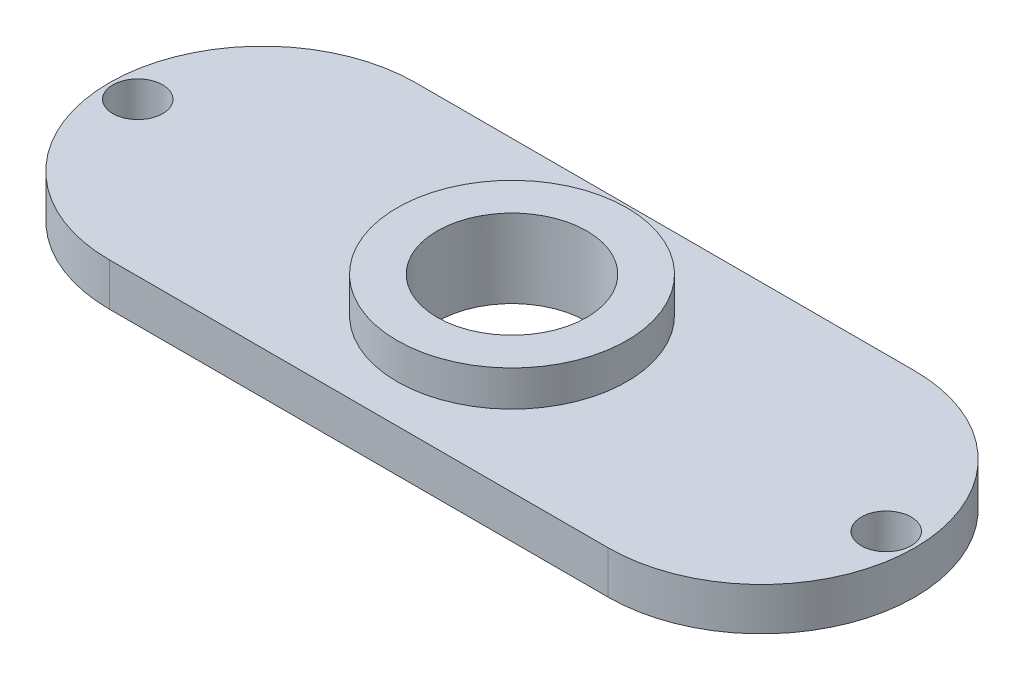
SolidWorks part; units mm, degrees
ref_plane "정면" through (0, 0, 0) normal (0, 0, 1) x (1, 0, 0)
ref_plane "윗면" through (0, 0, 0) normal (0, 1, 0) x (1, 0, 0)
ref_plane "우측면" through (0, 0, 0) normal (1, 0, 0) x (0, 0, -1)
sketch "스케치1" plane through (0, 0, 0) normal (0, 1, 0) x (1, 0, 0)
  circle A0 centre (0, 0) radius 4.2
  circle A1 centre (0, 0) radius 6.45
  dimension "D1" = 8.4
  dimension "D2" = 12.9
extrude "보스-돌출1" add sketch "스케치1" along normal blind 2
sketch "스케치2" plane through (0, 0, 0) normal (0, -1, 0) x (1, 0, 0)
  line L0 (-14, 0) -> (14, 0) construction
  line L1 (-14, 8.6) -> (14, 8.6)
  line L2 (-14, -8.6) -> (14, -8.6)
  arc A0 (-14, 8.6) -> (-14, -8.6) centre (-14, 0) ccw
  arc A1 (14, -8.6) -> (14, 8.6) centre (14, 0) ccw
  circle A5 centre (0, 0) radius 4.2 construction
  circle A6 centre (0, 0) radius 4.2
  point P2 (0, 0)
  dimension "D1" = 17.2
  dimension "D2" = 28
extrude "보스-돌출3" add sketch "스케치2" along normal blind 2.4
sketch "스케치3" plane through (0, -2.4, 0) normal (0, -1, 0) x (1, 0, 0)
  line L0 (1.1, 0) -> (-1.1, 0) construction
  circle A0 centre (-21, 0) radius 1.4
  dimension "D1" = 21
  dimension "D2" = 2.8
extrude "컷-돌출1" cut sketch "스케치3" against normal blind 10 contours A0
mirror "대칭 복사1" about plane through (0, 0, 0) normal (1, 0, 0) of "컷-돌출1"
